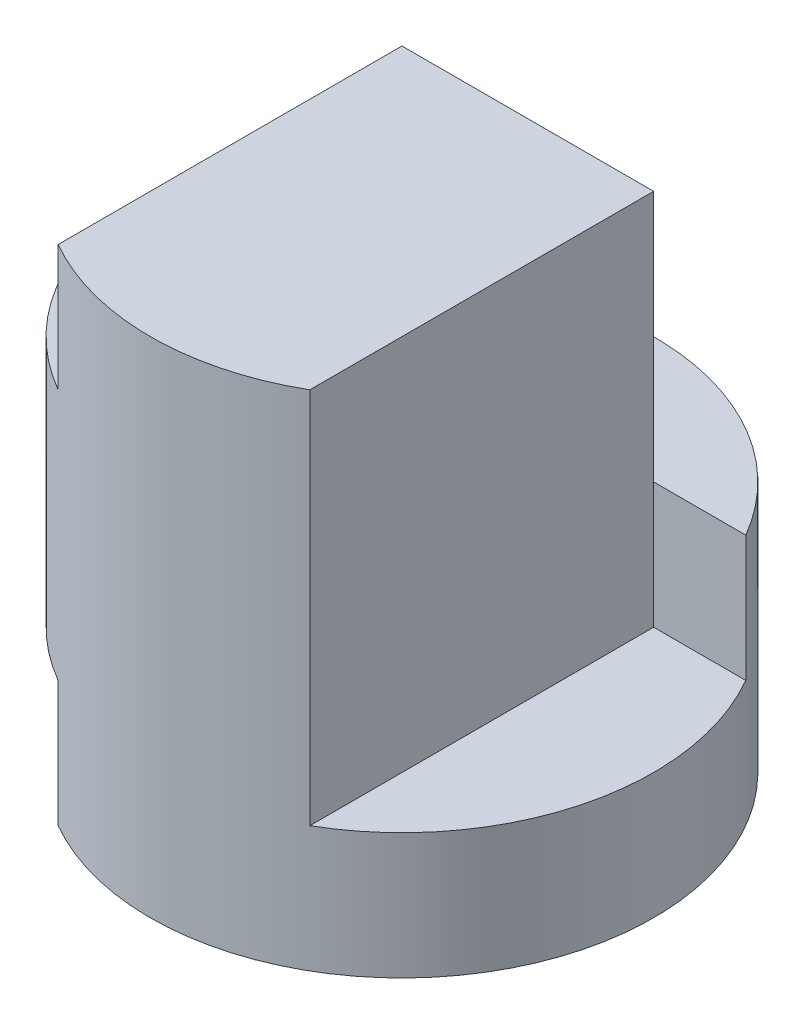
SolidWorks part; units mm, degrees
ref_plane "Front" through (0, 0, 0) normal (0, 0, 1) x (1, 0, 0)
ref_plane "Top" through (0, 0, 0) normal (0, 1, 0) x (1, 0, 0)
ref_plane "Right" through (0, 0, 0) normal (1, 0, 0) x (0, 0, -1)
sketch "Sketch1" plane through (0, 0, 0) normal (0, 1, 0) x (1, 0, 0)
  circle A0 centre (0, 0) radius 2
  dimension "D1" = 4
extrude "Boss-Extrude1" add sketch "Sketch1" along normal blind 4
sketch "Sketch2" plane through (0, 0, 0) normal (0, 0, 1) x (1, 0, 0)
  line L1 (-2, 4) -> (-1, 4)
  line L2 (-2, 4) -> (-2, 3)
  line L3 (-2, 3) -> (-1, 3)
  line L4 (-1, 4) -> (-1, 3)
  line L5 (2, 4) -> (1, 4)
  line L6 (2, 4) -> (2, 1)
  line L7 (2, 1) -> (1, 1)
  line L8 (1, 4) -> (1, 1)
  line L9 (-2, 0) -> (-1, 0)
  line L10 (-2, 0) -> (-2, 1)
  line L11 (-2, 1) -> (-1, 1)
  line L12 (-1, 0) -> (-1, 1)
  dimension "D1" = 1
  dimension "D2" = 1
  dimension "D3" = 1
  dimension "D4" = 3
  dimension "D5" = 1
  dimension "D6" = 1
extrude "Cut-Extrude1" cut sketch "Sketch2" against normal blind 1 and the other way blind 4
sketch "Sketch3" plane through (0, 4, 0) normal (0, 1, 0) x (1, 0, 0)
  line L0 (-1.7321, 1) -> (1.7321, 1)
  arc A0 (-1.7321, 1) -> (1.7321, 1) centre (0, 0) cw
extrude "Cut-Extrude2" cut sketch "Sketch3" against normal blind 2
